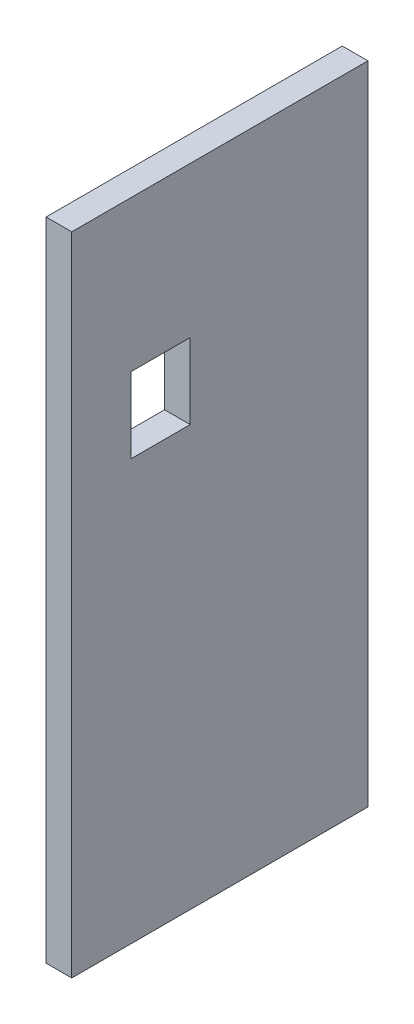
SolidWorks part; units mm, degrees
material "Oak"
ref_plane "Front Plane" through (0, 0, 0) normal (0, 0, 1) x (1, 0, 0)
ref_plane "Top Plane" through (0, 0, 0) normal (0, 1, 0) x (1, 0, 0)
ref_plane "Right Plane" through (0, 0, 0) normal (1, 0, 0) x (0, 0, -1)
sketch "Sketch1" plane through (0, 0, 0) normal (1, 0, 0) x (0, 0, -1)
  line L1 (-27.5, -60) -> (27.5, -60)
  line L2 (-27.5, -60) -> (-27.5, 60)
  line L3 (-27.5, 60) -> (27.5, 60)
  line L4 (27.5, -60) -> (27.5, 60)
  line L5 (-27.5, -60) -> (27.5, 60) construction
  line L6 (-27.5, 60) -> (27.5, -60) construction
  point P1 (0, 0)
  dimension "D1" = 120
  dimension "D2" = 55
extrude "Boss-Extrude1" add sketch "Sketch1" along normal blind 4.7625
sketch "Sketch2" plane through (0, 0, 0) normal (-1, 0, 0) x (0, 0, 1)
  line L0 (27.5, 60) -> (27.5, -60) construction
  line L1 (5.5, 32) -> (16.5, 32)
  line L2 (5.5, 32) -> (5.5, 18)
  line L3 (5.5, 18) -> (16.5, 18)
  line L4 (16.5, 32) -> (16.5, 18)
  line L5 (5.5, 32) -> (16.5, 18) construction
  line L6 (5.5, 18) -> (16.5, 32) construction
  line L8 (27.5, -60) -> (-27.5, -60) construction
  point P0 (11, 25)
  dimension "D1" = 11
  dimension "D2" = 14
  dimension "D3" = 11
  dimension "D4" = 78
extrude "Cut-Extrude1" cut sketch "Sketch2" against normal through all contours L3 L4 L1 L2
